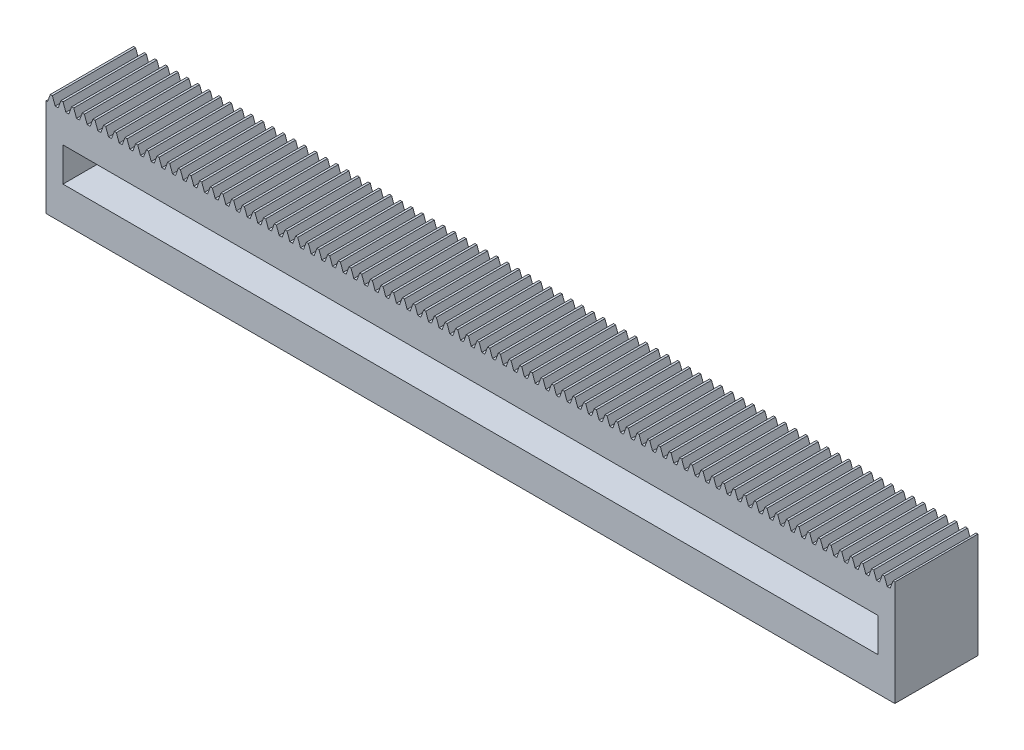
SolidWorks part; units mm, degrees
extrude "Blank" add sketch "BlankSke" against normal blind 24.5
sketch "BlankSke" plane through (0, 0, 0) normal (0, 0, 1) x (1, 0, 0)
  line L1 (0, 0) -> (250, 0)
  line L2 (0, 0) -> (0, 31)
  line L3 (0, 31) -> (250, 31)
  line L4 (250, 0) -> (250, 31)
  dimension "Length" = 250
  dimension "Blank_height" = 31
ref_plane "Plane1" through (0, 0, 0) normal (0, 0, 1) x (1, 0, 0)
ref_plane "Plane2" through (0, 0, 0) normal (0, 1, 0) x (1, 0, 0)
ref_plane "Plane3" through (0, 0, 0) normal (1, 0, 0) x (0, 0, -1)
other "Configuration Table"
sketch "HoldingSke" plane through (0, 0, 0) normal (0, 1, 0) x (1, 0, 0)
  line L0 (0, 0) -> (0.1392, 0.9903)
  line L1 (-15, 0) -> (100, 0) construction
  line L2 (0, 0) -> (-2.1039, 2.3779)
  line L3 (0, 0) -> (-11.863, 4.5341)
  line L4 (0, 0) -> (1.351, 8.5297)
  line L5 (0, 0) -> (-23.7986, -8.8762)
  line L6 (0, 0) -> (-10.5278, -7.1032)
  line L9 (-71.009, 38.7566) -> (163.9142, 124.2616)
  line L10 (-76.2, 3.3779) -> (-46.2, 3.3779)
  line L11 (0, 0) -> (-24.5, 0)
  line L12 (-76.2, 101.6) -> (-76.162, 101.6)
  line L13 (24.9733, 27.94) -> (52.9518, 28.4284)
  line L14 (24.9733, 27.94) -> (24.9743, 27.94)
  line L15 (24.9733, 27.94) -> (100.4006, 29.5858)
  circle A0 centre (0, 0) radius 19.05
  circle A1 centre (0, 0) radius 15
  circle A2 centre (0, 0) radius 12.7
  dimension "MPH" = 30
  dimension "Diameter" = 38.1
  dimension "Num_teeth" = 81
  dimension "Pitch" = 1
  dimension "Show_teeth" = 998
  dimension "Thickness" = 12.7
  dimension "Ap" = 20
  dimension "Pitch_height" = 30
  dimension "Width" = 24.5
  dimension "Backlash" = 0.038
  dimension "Addendum_fac" = 1
  dimension "Dedendum_fac" = 1.25
  dimension "Clearance_fac" = 0.25
  dimension "Dedendum_add" = 0.001
  dimension "Length" = 250
  dimension "Module" = 1
sketch "TooCutSkeIll" plane through (0, 0, 0) normal (0, 0, 1) x (1, 0, 0)
  line L0 (-1.2538, 30.9737) -> (-0.5045, 28.9152)
  line L1 (-0.2687, 28.75) -> (0.2687, 28.75)
  line L2 (0.5045, 28.9152) -> (1.2538, 30.9737)
  line L3 (250, 31) -> (0, 31) construction
  line L4 (0, 0) -> (0, 64.897) construction
  line L5 (-13.208, 30) -> (12.954, 30) construction
  line L6 (0, 0) -> (250, 0) construction
  line L7 (0.8994, 30) -> (0.8994, 48.7463) construction
  line L8 (-0.8994, 30) -> (-0.8994, 48.7463) construction
  line L9 (1.2914, 31) -> (1.2914, 31.0254)
  line L10 (-1.2914, 31) -> (-1.2914, 31.0254)
  line L11 (-1.2914, 31.0254) -> (1.2914, 31.0254)
  arc A0 (0.2687, 28.75) -> (0.5045, 28.9152) centre (0.2687, 29.001) ccw
  arc A1 (-0.5045, 28.9152) -> (-0.2687, 28.75) centre (-0.2687, 29.001) ccw
  arc A2 (1.2914, 31) -> (1.2538, 30.9737) centre (1.2914, 30.96) ccw
  arc A3 (-1.2538, 30.9737) -> (-1.2914, 31) centre (-1.2914, 30.96) ccw
  dimension "Pitch_height" = 30
  dimension "Addendum_plus" = 1.0254
  dimension "Pressure_angle" = 20
  dimension "Gap_width" = 1.7988
  dimension "Dedendum" = 1.25
extrude "ToothCutIll" [suppressed] cut sketch "TooCutSkeIll" against normal through all
sketch "TooCutSkeSim" plane through (0, 0, 0) normal (0, 0, 1) x (1, 0, 0)
  line L0 (0.4444, 28.75) -> (-0.4444, 28.75)
  line L1 (1.2726, 31.0254) -> (0.4444, 28.75)
  line L2 (0, 17.4625) -> (0, 53.467) construction
  line L3 (1.2726, 31.0254) -> (-1.2726, 31.0254)
  line L6 (-1.2726, 31.0254) -> (-0.4444, 28.75)
  line L9 (-0.8994, 30) -> (0.8994, 30) construction
  line L10 (0, 0) -> (250, 0) construction
  line L11 (0.8994, 30) -> (0.8994, 53.467) construction
  line L12 (-0.8994, 30) -> (-0.8994, 53.467) construction
  dimension "Pitch_height" = 30
  dimension "Addendum_plus" = 1.0254
  dimension "Pressure_angle" = 20
  dimension "Gap_width" = 1.7988
  dimension "Dedendum" = 1.25
extrude "ToothCutSim" cut sketch "TooCutSkeSim" against normal through all
pattern_linear "TeethCuts" count 80 spacing 3.1416 along (1, 0, 0) of "ToothCutIll", "ToothCutSim"
sketch "Sketch1" plane through (0, 0, 0) normal (0, 0, 1) x (1, 0, 0)
  line L0 (0, 15) -> (250, 15) construction
  line L1 (0, 28.75) -> (0, 0) construction
  line L2 (250, 0) -> (250, 31) construction
  line L3 (0, 0) -> (250, 0) construction
  line L5 (5, 20) -> (245, 20)
  line L6 (5, 20) -> (5, 10)
  line L7 (5, 10) -> (245, 10)
  line L8 (245, 20) -> (245, 10)
  line L9 (5, 20) -> (245, 10) construction
  line L10 (5, 10) -> (245, 20) construction
  point P8 (125, 15)
  dimension "D1" = 15
  dimension "D2" = 10
  dimension "D3" = 5
extrude "Cut-Extrude1" cut sketch "Sketch1" against normal up to surface (24.5 mm away) up to face at (124.8802, 29.6894, -24.5)
equation "' \"Module@HoldingSke\" = 6.35"
equation "' \"Num_teeth@HoldingSke\" = 12"
equation "' \"Ap@HoldingSke\" =  20"
equation "' \"Ap@HoldingSke\" = 20"
equation "' \"Width@HoldingSke\" = 0.25 * 25.4"
equation "' \"Show_teeth@HoldingSke\" = 500"
equation "' \"Backlash@HoldingSke\" = 0.009 * 25.4"
equation "' \"Addendum_fac@HoldingSke\" = 1.0"
equation "' \"Dedendum_fac@HoldingSke\" = 1.25"
equation "' \"Dedendum_add@HoldingSke\" = 0.00005 * 25.4"
equation "' \"Clearance_fac@HoldingSke\" = 0.25"
equation "' \"Pitch_height@HoldingSke\" = 1 * 25.4"
equation "' \"Length@HoldingSke\" = 4.71 * 25.4"
equation "\"Pitch@HoldingSke\" = 1 / \"Module@HoldingSke\""
equation "\"MPH@HoldingSke\" = \"Dedendum_fac@HoldingSke\" / \"Pitch@HoldingSke\" + 2 * \"Dedendum_add@HoldingSke\" + 0.002 * 25.4"
equation "\"MPH@HoldingSke\" = ((sgn( \"MPH@HoldingSke\" - \"Pitch_height@HoldingSke\")+1)*( \"MPH@HoldingSke\" - \"Pitch_height@HoldingSke\"))/2 + \"Pitch_height@HoldingSke\""
equation "\"Blank_height@BlankSke\" = \"Pitch_height@HoldingSke\" + \"Addendum_fac@HoldingSke\"  / \"Pitch@HoldingSke\" "
equation "\"Length@BlankSke\" =  \"Length@HoldingSke\""
equation "\"Face_width@Blank\" = \"Width@HoldingSke\""
equation "\"Pressure_angle@TooCutSkeIll\" = \"Ap@HoldingSke\""
equation "\"Addendum_plus@TooCutSkeIll\" =  \"Addendum_fac@HoldingSke\"  / \"Pitch@HoldingSke\" + 0.001 *25.4"
equation "\"Dedendum@TooCutSkeIll\" = \"Dedendum_fac@HoldingSke\"  / \"Pitch@HoldingSke\""
equation "\"Pitch_height@TooCutSkeIll\" =  \"MPH@HoldingSke\""
equation "\"Gap_width@TooCutSkeIll\" = 3.14159265 / 2 / \"Pitch@HoldingSke\" + 6 * \"Backlash@HoldingSke\""
equation "\"Pressure_angle@TooCutSkeSim\" = \"Ap@HoldingSke\""
equation "\"Addendum_plus@TooCutSkeSim\" =  \"Addendum_fac@HoldingSke\"  / \"Pitch@HoldingSke\" + 0.001 * 25.4"
equation "\"Dedendum@TooCutSkeSim\" = \"Dedendum_fac@HoldingSke\"  / \"Pitch@HoldingSke\""
equation "\"Pitch_height@TooCutSkeSim\" =  \"MPH@HoldingSke\""
equation "\"Gap_width@TooCutSkeSim\" = 3.14159265 / 2 / \"Pitch@HoldingSke\" + 6 * \"Backlash@HoldingSke\""
equation "\"Root_fillet@TooCutSkeIll\" = \"Clearance_fac@HoldingSke\" / \"Pitch@HoldingSke\" + \"Dedendum_add@HoldingSke\""
equation "\"Break_rad@TooCutSkeIll\" = 0.02 / \"Pitch@HoldingSke\" * 2"
equation "\"Linear_pitch@TeethCuts\" = 3.14159265 / \"Pitch@HoldingSke\""
equation "\"Num_teeth@HoldingSke\" = int( ( \"Length@HoldingSke\" + 0 ) / (3.14159265 / \"Pitch@HoldingSke\")) + 0.9999  + 1"
equation " \"Num_teeth@TeethCuts\" = int( \"Show_teeth@HoldingSke\" ) + 1"
equation " \"Num_teeth@TeethCuts\" = ((sgn( \"Num_teeth@TeethCuts\" - \"Num_teeth@HoldingSke\" )-1)*( \"Num_teeth@TeethCuts\" - \"Num_teeth@HoldingSke\" ))/-2+ \"Num_teeth@HoldingSke\""
equation " \"Num_teeth@TeethCuts\" = ((sgn( \"Num_teeth@TeethCuts\" - 2.0)+1)*( \"Num_teeth@TeethCuts\" - 2.0))/2 +2.0"
